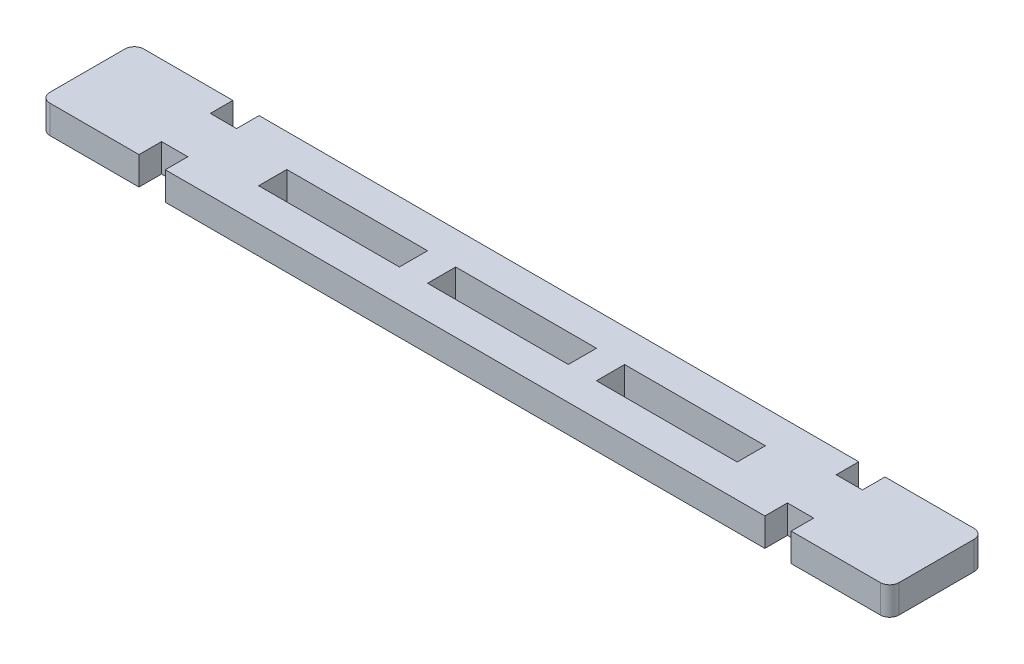
SolidWorks part; units mm, degrees
ref_plane "Front Plane" through (0, 0, 0) normal (0, 0, 1) x (1, 0, 0)
ref_plane "Top Plane" through (0, 0, 0) normal (0, 1, 0) x (1, 0, 0)
ref_plane "Right Plane" through (0, 0, 0) normal (1, 0, 0) x (0, 0, -1)
sketch "Sketch1" plane through (0, 0, 0) normal (0, 1, 0) x (1, 0, 0)
  line L1 (-90.5, 10) -> (90.5, 10)
  line L2 (-90.5, 10) -> (-90.5, -10)
  line L3 (-90.5, -10) -> (90.5, -10)
  line L4 (90.5, 10) -> (90.5, -10)
  line L5 (-90.5, 10) -> (90.5, -10) construction
  line L6 (-90.5, -10) -> (90.5, 10) construction
  point P0 (0, 0)
  dimension "D2" = 20
  dimension "D1" = 181
sketch "Sketch2" plane through (0, 0, 0) normal (0, 0, 1) x (1, 0, 0)
  line L0 (0, 0) -> (0, 6) construction
  line L1 (-90.5, 0) -> (90.5, 0) construction
  dimension "D1" = 6
extrude "Boss-Extrude1" add sketch "Sketch1" along normal up to vertex (6 mm away) contours L2 L3 L4 L1 up to point (0, 6, 0)
sketch "Sketch3" plane through (0, 6, 0) normal (0, 1, 0) x (1, 0, 0)
  line L0 (15, -3) -> (15, 3) construction
  line L1 (51, 3) -> (21, 3)
  line L2 (51, 3) -> (51, -3)
  line L3 (51, -3) -> (21, -3)
  line L4 (21, 3) -> (21, -3)
  line L5 (15, -3) -> (-15, -3)
  line L6 (15, -3) -> (15, 3)
  line L7 (15, 3) -> (-15, 3)
  line L8 (-15, -3) -> (-15, 3)
  line L10 (-51, 3) -> (-21, 3)
  line L11 (-51, 3) -> (-51, -3)
  line L12 (-51, -3) -> (-21, -3)
  line L13 (-21, 3) -> (-21, -3)
extrude "Cut-Extrude1" cut sketch "Sketch3" against normal through all
sketch "Sketch4" plane through (0, 0, 0) normal (0, -1, 0) x (1, 0, 0)
  line L0 (-90.5, 10) -> (90.5, 10) construction
  line L1 (-69.7, 10) -> (-63.7, 10)
  line L2 (-69.7, 10) -> (-69.7, 5)
  line L3 (-69.7, 5) -> (-63.7, 5)
  line L4 (-63.7, 10) -> (-63.7, 5)
  line L5 (-90.5, -10) -> (90.5, -10) construction
  line L6 (-69.7, -5) -> (-63.7, -5)
  line L7 (-69.7, -5) -> (-69.7, -10)
  line L8 (-69.7, -10) -> (-63.7, -10)
  line L9 (-63.7, -5) -> (-63.7, -10)
  line L10 (-132.2288, -186.9719) -> (-132.2288, -171.9719) construction
  line L11 (-61, 3) -> (-61, -3) construction
  line L12 (-240.7288, -195.9719) -> (-234.7288, -189.9719) construction
  line L13 (-61, 3) -> (-61, -3) construction
  line L14 (-63.7, 5) -> (-63.7, 0) construction
  line L15 (-63.7, 0) -> (-63.7, -5) construction
  dimension "D1" = 62.5288
extrude "Cut-Extrude2" cut sketch "Sketch4" against normal through all
mirror "Mirror1" about plane through (0, 0, 0) normal (1, 0, 0) of "Cut-Extrude2"
fillet "Fillet1" radius 2 4 edges at (90.5, 3, 10) (90.5, 3, -10) (-90.5, 3, -10) (-90.5, 3, 10)
sketch "Sketch5" plane through (0, 6, 0) normal (0, 1, 0) x (1, 0, 0)
  line L0 (-69.5, 9.8) -> (-63.9, 9.8)
  line L1 (-69.7, 10) -> (-63.7, 10)
  line L2 (-69.7, 10) -> (-69.7, 5)
  line L3 (-69.7, 5) -> (-63.7, 5)
  line L4 (-63.7, 10) -> (-63.7, 5)
  line L5 (-63.9, 9.8) -> (-63.9, 5.2)
  line L6 (-69.5, 5.2) -> (-63.9, 5.2)
  line L7 (-69.5, 9.8) -> (-69.5, 5.2)
  line L8 (-69.5, 9.8) -> (-69.5, 10)
  line L9 (-63.9, 9.8) -> (-63.9, 10)
  line M30 (-63.7, 10) -> (-63.7, 5)
  line M31 (-63.7, 5) -> (-69.7, 5)
  line M32 (-69.7, 5) -> (-69.7, 10)
  dimension "D1" = 0.2
extrude "Boss-Extrude2" add sketch "Sketch5" against normal up to surface (6 mm away) contours L9 L5 L6 L7 L8 L1 M32 M31 M30 up to face at (36, 0, 0)
mirror "Mirror2" about plane through (0, 0, 0) normal (1, 0, 0) of "Boss-Extrude2" second plane through (0, 0, 0) second plane normal (0, 0, 1)
equation "\"glass_width\"= 181"
equation "\"glass_height\"= 151"
equation "\"glass_thickness\"= 2.5"
equation "\"brood_space\"= 42"
equation "\"t1\"= 6"
equation "\"t2\"= 6"
equation "\"box_depth\"= \"brood_space\" + \"glass_thickness\" + \"glass_thickness\" + \"t2\" + \"t2\""
equation "\"box_width\"= \"glass_width\" + \"t1\" + \"t1\""
equation "\"food_height\"= 70"
equation "\"box_height\"= \"glass_height\" + ( \"t1\" * 3 ) + \"food_height\""
equation "\"D1@Sketch2\"=\"t1\""
equation "\"D1@Sketch1\"=\"glass_width\""
equation "\"entry_height\"= 24"
equation "\"entry_diameter\"= 8"
equation "\"food_top_clearance\"= 10"
equation "\"bar_width\"= 20"
equation "\"glassblocker_lower_height\"= 10"
equation "\"lower_edge_stickout\"=6"
